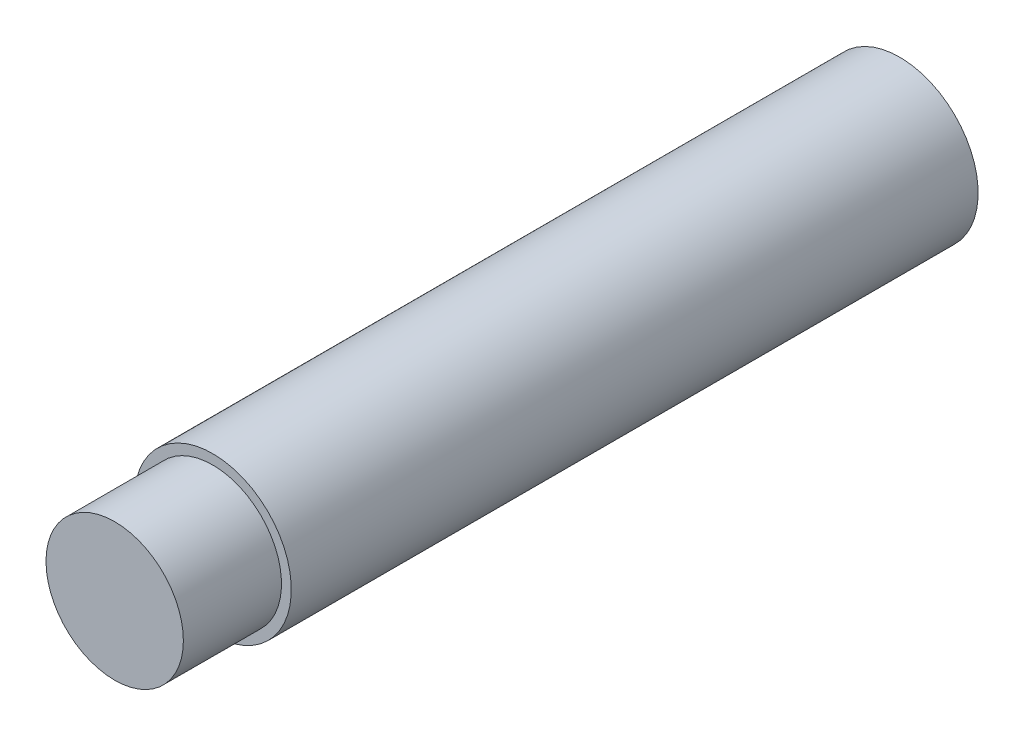
SolidWorks part; units mm, degrees
ref_plane "前视基准面" through (0, 0, 0) normal (0, 0, 1) x (1, 0, 0)
ref_plane "上视基准面" through (0, 0, 0) normal (0, 1, 0) x (1, 0, 0)
ref_plane "右视基准面" through (0, 0, 0) normal (1, 0, 0) x (0, 0, -1)
sketch "草图1" plane through (0, 0, 0) normal (0, 0, 1) x (1, 0, 0)
  circle A0 centre (0, 0) radius 5.25
  dimension "D1" = 10.5
extrude "凸台-拉伸1" add sketch "草图1" along normal blind 7.5
sketch "草图2" plane through (0, 0, 0) normal (0, 0, -1) x (-1, 0, 0)
  circle A0 centre (0, 0) radius 6
extrude "凸台-拉伸2" add sketch "草图2" along normal blind 42.5
cosmetic thread "装饰螺纹线1" parameters "D1"=42.5, "D2"=6.647
sketch "草图3" plane through (0, 0, -42.5) normal (0, 0, -1) x (-1, 0, 0)
  circle A0 centre (0, 0) radius 6
extrude "凸台-拉伸3" add sketch "草图3" along normal blind 10
